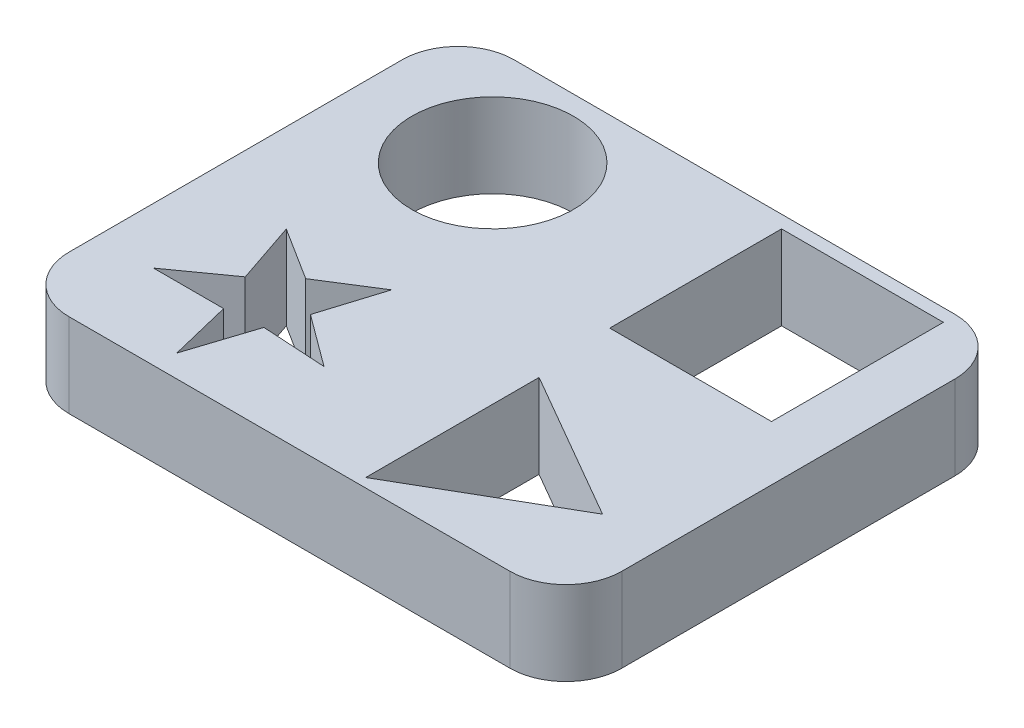
SolidWorks part; units mm, degrees
ref_plane "Front Plane" through (0, 0, 0) normal (0, 0, 1) x (1, 0, 0)
ref_plane "Top Plane" through (0, 0, 0) normal (0, 1, 0) x (1, 0, 0)
ref_plane "Right Plane" through (0, 0, 0) normal (1, 0, 0) x (0, 0, -1)
sketch "Sketch1" plane through (0, 0, 0) normal (0, 1, 0) x (1, 0, 0)
  line L0 (-26.1101, 13.0076) -> (-27.4792, 18.6293)
  line L1 (-33.8538, 51.3612) -> (6.1512, 51.3612)
  line L2 (-38.9338, 46.2812) -> (-38.9338, 16.0552)
  line L3 (-33.8538, 10.9752) -> (6.1512, 10.9752)
  line L4 (11.2312, 46.2812) -> (11.2312, 16.0552)
  line L5 (6.2552, 50.208) -> (-8.4285, 50.208)
  line L6 (6.2552, 50.208) -> (6.2552, 34.6136)
  line L7 (6.2552, 34.6136) -> (-8.4285, 34.6136)
  line L8 (-8.4285, 50.208) -> (-8.4285, 34.6136)
  line L9 (5.8676, 19.6653) -> (-7.7583, 27.5322)
  line L10 (-7.7583, 27.5322) -> (-7.7583, 11.7984)
  line L11 (-7.7583, 11.7984) -> (5.8676, 19.6653)
  line L17 (-27.4792, 18.6293) -> (-33.8477, 18.6293)
  line L18 (-30.8922, 27.7254) -> (-26.1101, 24.7053)
  line L19 (-26.1101, 24.7053) -> (-21.328, 27.7254)
  line L20 (-33.8477, 18.6293) -> (-28.9933, 22.1037)
  line L21 (-28.9933, 22.1037) -> (-30.8922, 27.7254)
  line L22 (-26.1101, 13.0076) -> (-24.1712, 18.9749)
  line L23 (-24.1712, 18.9749) -> (-18.3725, 18.6293)
  line L24 (-18.3725, 18.6293) -> (-23.0764, 22.1037)
  line L25 (-23.0764, 22.1037) -> (-21.328, 27.7254)
  arc A0 (6.1512, 51.3612) -> (11.2312, 46.2812) centre (6.1512, 46.2812) cw
  arc A1 (6.1512, 10.9752) -> (11.2312, 16.0552) centre (6.1512, 16.0552) ccw
  arc A2 (-38.9338, 16.0552) -> (-33.8538, 10.9752) centre (-33.8538, 16.0552) ccw
  arc A3 (-33.8538, 51.3612) -> (-38.9338, 46.2812) centre (-33.8538, 46.2812) ccw
  circle A4 centre (-3.2163, 19.6653) radius 4.542 construction
  circle A5 centre (-26.7288, 42.2881) radius 7.3385
  point P7 (11.2312, 51.3612)
  point P12 (-38.9338, 10.9752)
  point P15 (-38.9338, 51.3612)
  point P26 (-23.2451, 22.1037)
  point P27 (-26.1101, 25.3956)
  point P34 (-22.3907, 22.1037)
  point P39 (-28.9933, 22.1037)
  point P40 (-23.0764, 22.1037)
  point P41 (-26.1101, 24.7053)
  point P42 (0, 0)
  dimension "D2" = 50.165
  dimension "D3" = 5.08
  dimension "D1" = 40.386
  dimension "D4" = 14.6837
  dimension "D5" = 1.1532
extrude "Boss-Extrude6" add sketch "Sketch1" along normal blind 7.62
